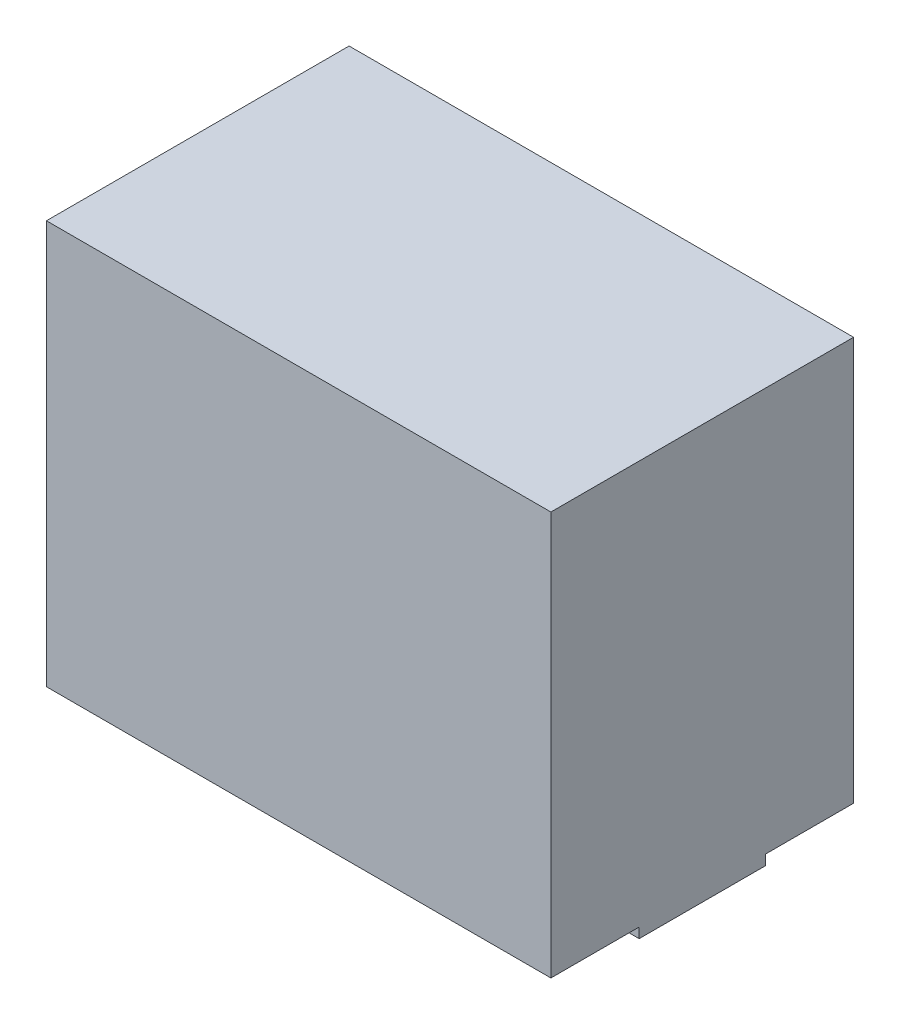
SolidWorks part; units mm, degrees
ref_plane "Front Plane" through (0, 0, 0) normal (0, 0, 1) x (1, 0, 0)
ref_plane "Top Plane" through (0, 0, 0) normal (0, 1, 0) x (1, 0, 0)
ref_plane "Right Plane" through (0, 0, 0) normal (1, 0, 0) x (0, 0, -1)
sketch "Sketch1" plane through (0, 0, 0) normal (0, 1, 0) x (1, 0, 0)
  line L1 (0, 0) -> (1, 0)
  line L2 (0, 0) -> (0, 0.6)
  line L3 (0, 0.6) -> (1, 0.6)
  line L4 (1, 0) -> (1, 0.6)
  dimension "D1" = 1
  dimension "D2" = 0.6
extrude "Boss-Extrude1" add sketch "Sketch1" along normal blind 0.8 contours L2 L3 L4 L1
sketch "Sketch3" plane through (0, 0, 0) normal (0, -1, 0) x (1, 0, 0)
  line L0 (0, 0) -> (0, -0.6) construction
  line L1 (0, -0.175) -> (0.2, -0.175)
  line L2 (0, -0.175) -> (0, -0.425)
  line L3 (0, -0.425) -> (0.2, -0.425)
  line L4 (0.2, -0.175) -> (0.2, -0.425)
  line L5 (1, -0.175) -> (0.8, -0.175)
  line L6 (1, -0.175) -> (1, -0.425)
  line L7 (1, -0.425) -> (0.8, -0.425)
  line L8 (0.8, -0.175) -> (0.8, -0.425)
  line L9 (1, 0) -> (1, -0.6) construction
  line L10 (0.2, -0.175) -> (0, -0.425) construction
  line L11 (0, -0.175) -> (0.2, -0.425) construction
  line L12 (0, 0) -> (1, -0.6) construction
  line L13 (1, 0) -> (0, -0.6) construction
  line L14 (0.8, -0.175) -> (1, -0.425) construction
  line L16 (1, -0.175) -> (0.8, -0.425) construction
  point P29 (0.1, -0.3)
  point P30 (0.5, -0.3)
  point P36 (0.9, -0.3)
  dimension "D1" = 0.2
  dimension "D2" = 0.25
extrude "Boss-Extrude2" add sketch "Sketch3" along normal blind 0.02
